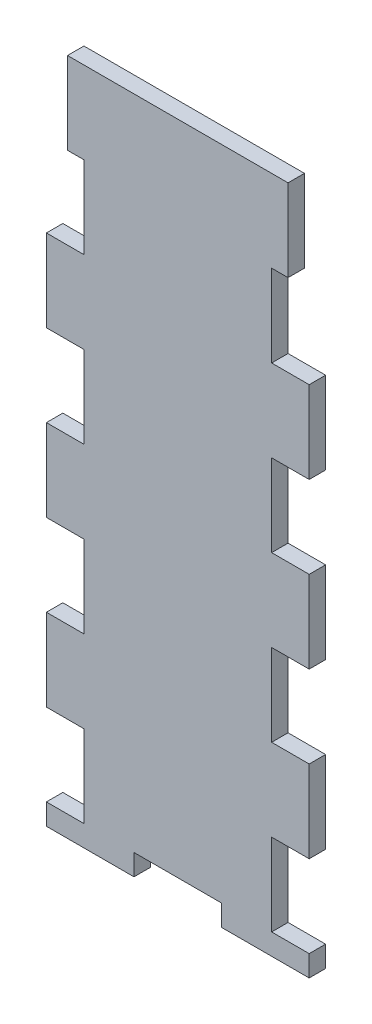
SolidWorks part; units mm, degrees
ref_plane "Front Plane" through (0, 0, 0) normal (0, 0, 1) x (1, 0, 0)
ref_plane "Top Plane" through (0, 0, 0) normal (0, 1, 0) x (1, 0, 0)
ref_plane "Right Plane" through (0, 0, 0) normal (1, 0, 0) x (0, 0, -1)
sketch "Sketch1" plane through (0, 0, 0) normal (0, 0, 1) x (1, 0, 0)
  line L0 (24, 61.25) -> (24, 52.5) construction
  line L1 (0, 0) -> (20, 0)
  line L2 (0, 0) -> (0, 70)
  line L3 (0, 70) -> (20, 70)
  line L4 (20, 0) -> (20, 70)
  line L13 (20, 70) -> (24, 70)
  line L18 (20, 70) -> (20, 61.25)
  line L19 (10, 0) -> (10, 70) construction
  line L20 (20, 61.25) -> (24, 61.25)
  line L21 (24, 70) -> (24, 61.25)
  line L42 (20, 52.5) -> (24, 52.5)
  line L43 (20, 52.5) -> (20, 43.75)
  line L44 (20, 43.75) -> (24, 43.75)
  line L45 (24, 52.5) -> (24, 43.75)
  line L46 (24, 43.75) -> (24, 35) construction
  line L47 (20, 35) -> (24, 35)
  line L48 (20, 35) -> (20, 26.25)
  line L49 (20, 26.25) -> (24, 26.25)
  line L50 (24, 35) -> (24, 26.25)
  line L51 (24, 26.25) -> (24, 17.5) construction
  line L52 (20, 17.5) -> (24, 17.5)
  line L53 (20, 17.5) -> (20, 8.75)
  line L54 (20, 8.75) -> (24, 8.75)
  line L55 (24, 17.5) -> (24, 8.75)
  line L56 (24, 8.75) -> (24, 0) construction
  line L57 (-4, 26.25) -> (-4, 17.5) construction
  line L58 (-4, 43.75) -> (-4, 35) construction
  line L59 (-4, 61.25) -> (-4, 52.5) construction
  line L60 (-4, 17.5) -> (-4, 8.75)
  line L61 (0, 8.75) -> (-4, 8.75)
  line L62 (0, 17.5) -> (0, 8.75)
  line L63 (0, 17.5) -> (-4, 17.5)
  line L64 (-4, 35) -> (-4, 26.25)
  line L65 (0, 26.25) -> (-4, 26.25)
  line L66 (0, 35) -> (0, 26.25)
  line L67 (0, 35) -> (-4, 35)
  line L68 (-4, 52.5) -> (-4, 43.75)
  line L69 (0, 43.75) -> (-4, 43.75)
  line L70 (0, 52.5) -> (0, 43.75)
  line L71 (0, 52.5) -> (-4, 52.5)
  line L72 (-4, 70) -> (-4, 61.25)
  line L73 (0, 61.25) -> (-4, 61.25)
  line L74 (0, 70) -> (0, 61.25)
  line L75 (0, 70) -> (-4, 70)
  dimension "D1" = 20
  dimension "D2" = 70
  dimension "D4" = 4
  dimension "D3" = 4
extrude "Boss-Extrude1" add sketch "Sketch1" along normal blind 1.75
sketch "Sketch2" plane through (0, 0, 0) normal (0, 0, -1) x (-1, 0, 0)
  line L0 (0, 0) -> (-20, 0) construction
  line L1 (4, 0) -> (-24, 0)
  line L2 (4, 0) -> (4, -2.25)
  line L3 (4, -2.25) -> (-24, -2.25)
  line L4 (-24, 0) -> (-24, -2.25)
  line L6 (-24, 17.5) -> (-24, 8.75) construction
  line L7 (4, 17.5) -> (4, 8.75) construction
  dimension "D1" = 2.25
extrude "Boss-Extrude2" add sketch "Sketch2" against normal up to surface (1.75 mm away) up to face at (10, 35, 1.75)
sketch "Sketch3" plane through (0, 0, 1.75) normal (0, 0, 1) x (1, 0, 0)
  line L0 (24, -2.25) -> (-4, -2.25) construction
  line L1 (14.6667, -2.25) -> (5.3333, -2.25)
  line L2 (14.6667, -2.25) -> (14.6667, 0)
  line L3 (14.6667, 0) -> (5.3333, 0)
  line L4 (5.3333, -2.25) -> (5.3333, 0)
  line L5 (10, -2.25) -> (10, 70) construction
  line L6 (-4, 70) -> (24, 70) construction
  line L7 (14.6667, 0) -> (24, 0) construction
  line L8 (24, 0) -> (24, -2.25) construction
  line L9 (5.3333, 0) -> (-4, 0) construction
  line L10 (-4, -2.25) -> (-4, 0) construction
  line L11 (20, 0) -> (24, 0) construction
  point P6 (10, 0)
extrude "Cut-Extrude1" cut sketch "Sketch3" against normal through all
sketch "Sketch4" plane through (0, 0, 1.75) normal (0, 0, 1) x (1, 0, 0)
  line L0 (0, 61.25) -> (-4, 61.25) construction
  line L1 (-4, 70) -> (-1.75, 70)
  line L2 (-4, 70) -> (-4, 61.25)
  line L3 (-4, 61.25) -> (-1.75, 61.25)
  line L4 (-1.75, 70) -> (-1.75, 61.25)
  line L5 (20, 61.25) -> (24, 61.25) construction
  line L6 (24, 70) -> (21.75, 70)
  line L7 (24, 70) -> (24, 61.25)
  line L8 (24, 61.25) -> (21.75, 61.25)
  line L9 (21.75, 70) -> (21.75, 61.25)
  dimension "D1" = 2.25
extrude "Cut-Extrude2" cut sketch "Sketch4" against normal through all
equation "\"D1@Boss-Extrude1\"=\"thick\""
equation "\"D4@Sketch1\"=\"thick\"*2 + \"veneer_thickness\""
equation "\"D1@Sketch2\"=\"thick\" + \"veneer_thickness\""
equation "\"D1@Sketch4\"=\"thick\"+\"veneer_thickness\""
equation "\"veneer_thickness\"= 0.5mm"
equation "\"thick\"= 1.75mm"
